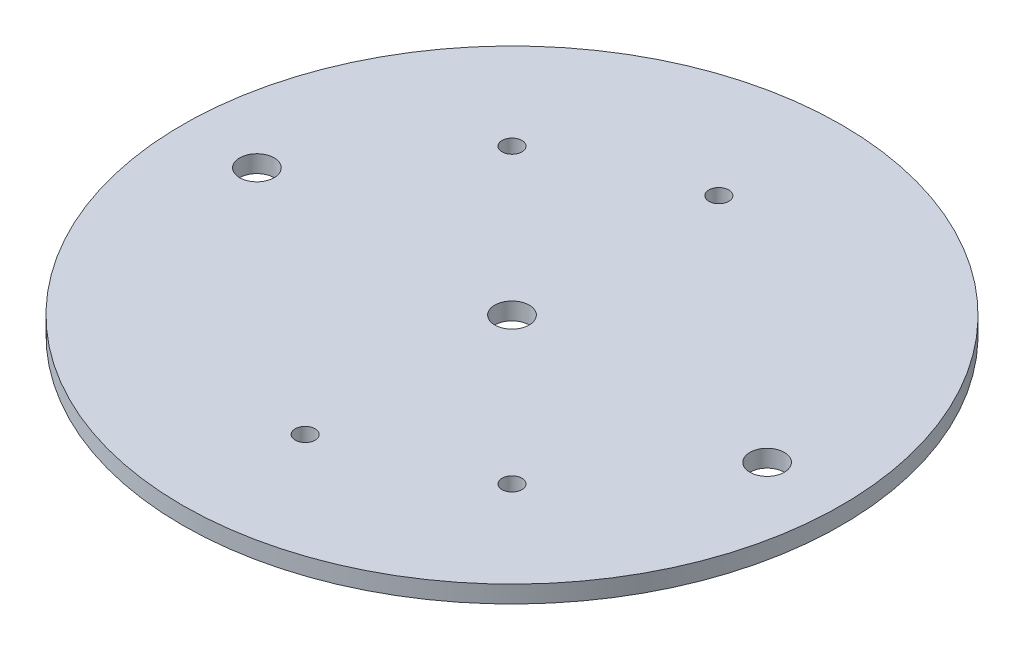
SolidWorks part; units mm, degrees
ref_plane "Front Plane" through (0, 0, 0) normal (0, 0, 1) x (1, 0, 0)
ref_plane "Top Plane" through (0, 0, 0) normal (0, 1, 0) x (1, 0, 0)
ref_plane "Right Plane" through (0, 0, 0) normal (1, 0, 0) x (0, 0, -1)
sketch "Sketch2" plane through (0, 0, 0) normal (0, 1, 0) x (1, 0, 0)
  line L0 (-46.99, 0) -> (46.99, 0) construction
  line L1 (0, -38.1) -> (0, 38.1) construction
  line L2 (-26.9408, 26.9408) -> (26.9408, -26.9408) construction
  circle A0 centre (0, 0) radius 60.706
  circle A1 centre (-46.99, 0) radius 3.175
  circle A2 centre (46.99, 0) radius 3.175
  circle A3 centre (0, 0) radius 3.175
  circle A4 centre (0, 38.1) radius 1.8288
  circle A5 centre (0, -38.1) radius 1.8288
  circle A8 centre (-26.9408, 26.9408) radius 1.8288
  circle A9 centre (26.9408, -26.9408) radius 1.8288
  point P6 (0, 0)
  point P12 (0, 0)
  point P17 (0, 0)
  point P18 (0, 0)
  dimension "D1" = 121.412
  dimension "D3" = 6.35
  dimension "D4" = 6.35
  dimension "D5" = 3.6576
  dimension "D6" = 76.2
  dimension "D8" = 45
  dimension "D2" = 93.98
  dimension "D7" = 76.2
extrude "Boss-Extrude1" add sketch "Sketch2" along normal blind 3.175
